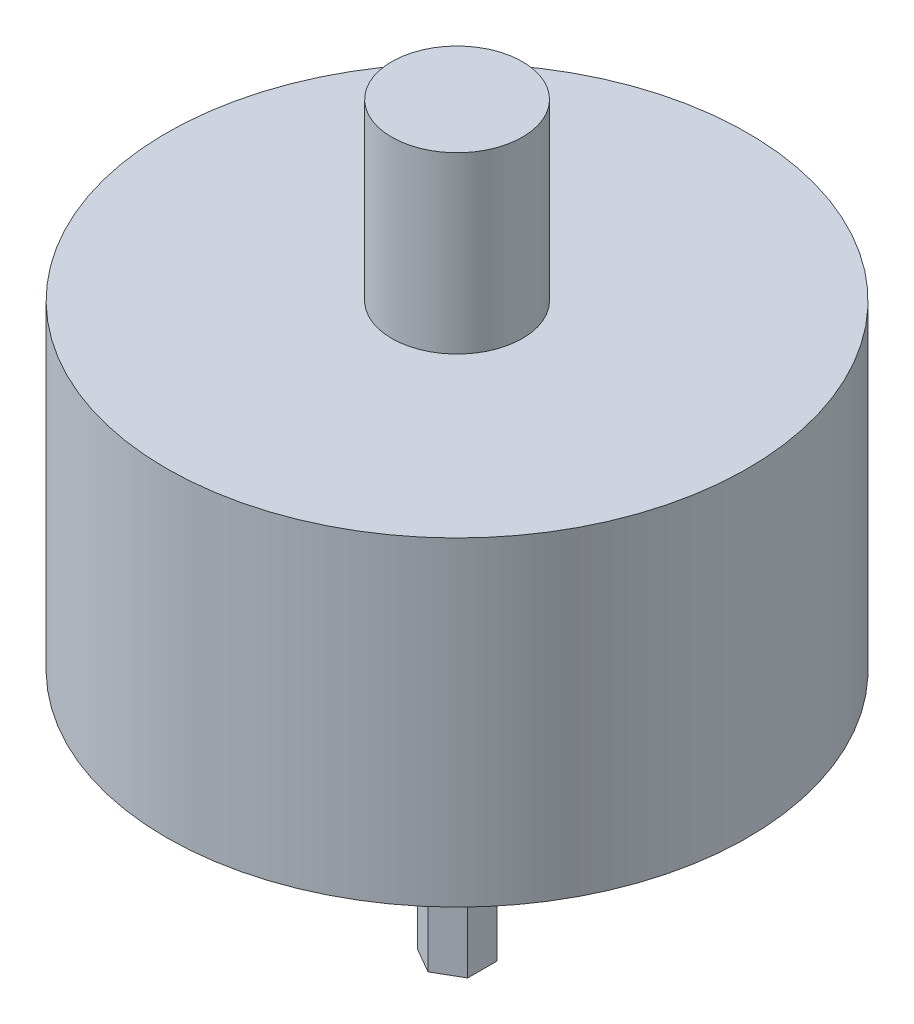
SolidWorks part; units mm, degrees
ref_plane "Front Plane" through (0, 0, 0) normal (0, 0, 1) x (1, 0, 0)
ref_plane "Top Plane" through (0, 0, 0) normal (0, 1, 0) x (1, 0, 0)
ref_plane "Right Plane" through (0, 0, 0) normal (1, 0, 0) x (0, 0, -1)
sketch "Sketch1" plane through (0, 0, 0) normal (0, 1, 0) x (1, 0, 0)
  line L19 (0, 1) -> (-0.866, 0.5)
  line L20 (-0.866, 0.5) -> (-0.866, -0.5)
  line L21 (-0.866, -0.5) -> (0, -1)
  line L22 (0, -1) -> (0.866, -0.5)
  line L23 (0.866, -0.5) -> (0.866, 0.5)
  line L24 (0.866, 0.5) -> (0, 1)
  circle A0 centre (0, 0) radius 0.866 construction
  point P1 (0, 0)
  dimension "D1" = 1
extrude "Boss-Extrude1" add sketch "Sketch1" along normal blind 8.5
sketch "Sketch2" plane through (0, 8.5, 0) normal (0, 1, 0) x (1, 0, 0)
  circle A0 centre (0, 0) radius 10
  point P2 (0, 0)
  point P3 (0, 0)
  dimension "D1" = 20
extrude "Boss-Extrude2" add sketch "Sketch2" along normal blind 11
sketch "Sketch3" plane through (0, 19.5, 0) normal (0, 1, 0) x (1, 0, 0)
  circle A0 centre (0, 0) radius 2.25
  point P2 (0, 0)
  point P3 (0, 0)
  dimension "D1" = 4.5
extrude "Boss-Extrude3" add sketch "Sketch3" along normal blind 6
